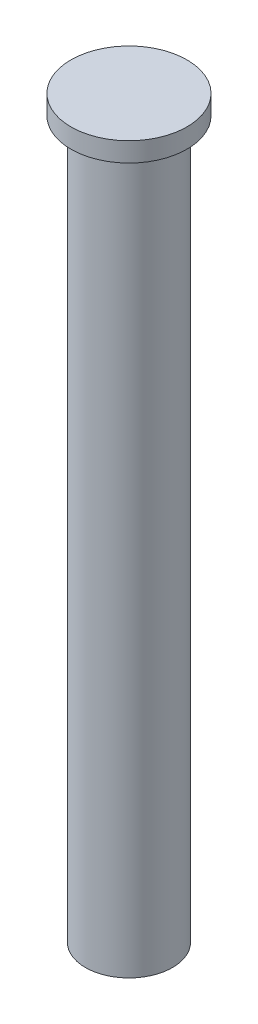
SolidWorks part; units mm, degrees
ref_plane "Plane1" through (0, 0, 0) normal (0, 0, 1) x (1, 0, 0)
ref_plane "Plane2" through (0, 0, 0) normal (0, 1, 0) x (1, 0, 0)
ref_plane "Plane3" through (0, 0, 0) normal (1, 0, 0) x (0, 0, -1)
other "Configuration Table"
sketch "Sketch2" plane through (0, 0, 0) normal (0, 0, 1) x (1, 0, 0)
  line L0 (0, 90) -> (0, -290) construction
  line L1 (0, 90) -> (0, -290)
  line L2 (22.5, -290) -> (0, -290)
  line L3 (22.5, -290) -> (22.5, 80)
  line L4 (0, 90) -> (30, 90)
  line L6 (30, 80) -> (22.5, 80)
  line L7 (30, 80) -> (30, 90)
  dimension "D1" = 22.5
  dimension "D2" = 380
  dimension "D3" = 10
  dimension "D4" = 30
revolve "Base-Revolve" add sketch "Sketch2" angle 360 about L0
